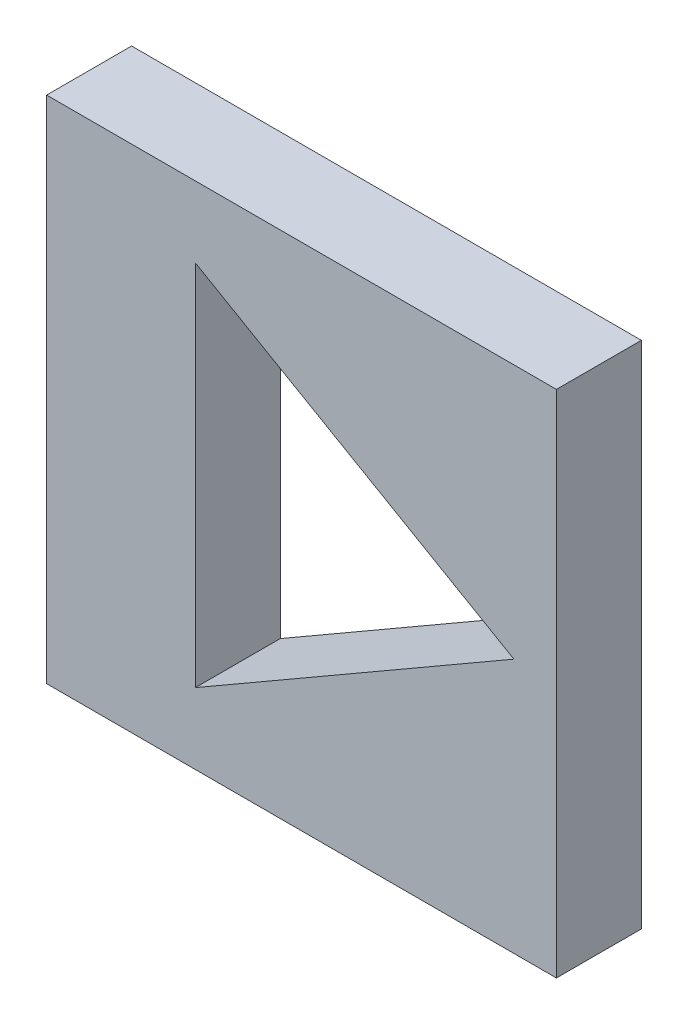
SolidWorks part; units mm, degrees
ref_plane "Piano frontale" through (0, 0, 0) normal (0, 0, 1) x (1, 0, 0)
ref_plane "Piano superiore" through (0, 0, 0) normal (0, 1, 0) x (1, 0, 0)
ref_plane "Piano destro" through (0, 0, 0) normal (1, 0, 0) x (0, 0, -1)
sketch "Schizzo1" plane through (0, 0, 0) normal (0, 0, 1) x (1, 0, 0)
  line L1 (-30, 30) -> (30, 30)
  line L2 (-30, 30) -> (-30, -30)
  line L3 (-30, -30) -> (30, -30)
  line L4 (30, 30) -> (30, -30)
  line L5 (25, 0) -> (-12.5, 21.6506)
  line L6 (-12.5, 21.6506) -> (-12.5, -21.6506)
  line L7 (-12.5, -21.6506) -> (25, 0)
  circle A0 centre (0, 0) radius 25 construction
  dimension "D1" = 60
  dimension "D2" = 60
  dimension "D3" = 30
  dimension "D4" = 30
extrude "Estrusione-Estrusione1" add sketch "Schizzo1" along normal blind 10 contours L5 L6 L7 | L1 L4 L3 L2
